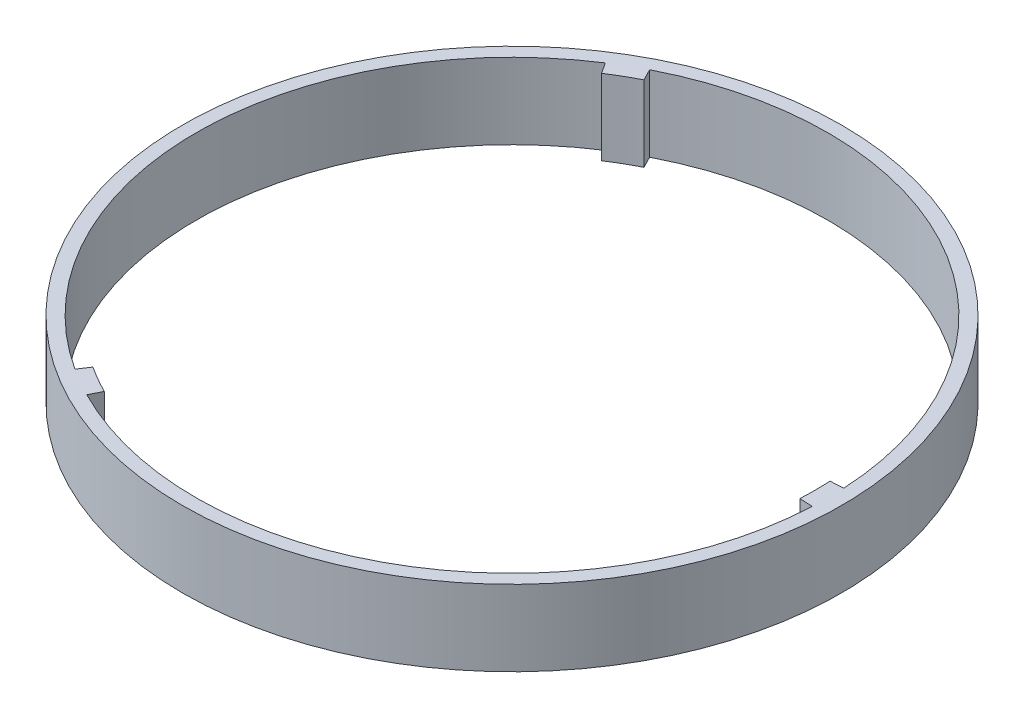
SolidWorks part; units mm, degrees
ref_plane "Front Plane" through (0, 0, 0) normal (0, 0, 1) x (1, 0, 0)
ref_plane "Top Plane" through (0, 0, 0) normal (0, 1, 0) x (1, 0, 0)
ref_plane "Right Plane" through (0, 0, 0) normal (1, 0, 0) x (0, 0, -1)
sketch "Sketch1" plane through (0, 0, 0) normal (0, 1, 0) x (1, 0, 0)
  circle A0 centre (0, 0) radius 110.49
  dimension "D1" = 220.98
extrude "Boss-Extrude1" add sketch "Sketch1" along normal blind 25.4
sketch "Sketch2" plane through (0, 25.4, 0) normal (0, 1, 0) x (1, 0, 0)
  circle A0 centre (0, 0) radius 101.6
extrude "Cut-Extrude6" cut sketch "Sketch2" against normal blind 64.52
sketch "Sketch5" plane through (0, 25.4, 0) normal (0, 1, 0) x (1, 0, 0)
  line L0 (-110.49, 0) -> (110.49, 0) construction
  line L1 (0, 0) -> (-55.2498, 95.6844) construction
  line L2 (0, 0) -> (-55.245, -95.6871) construction
  line L3 (-46.2337, -90.471) -> (-55.2333, -85.2751)
  line L5 (-46.2337, -90.471) -> (-55.2333, -85.2751) construction
  line L8 (-46.2337, -90.471) -> (-48.2094, -94.3533)
  line L9 (110.49, 0) -> (101.4685, 5.1668) construction
  line L10 (110.49, 0) -> (101.4785, -4.9664) construction
  line L11 (101.4685, 5.1668) -> (101.4785, -4.9664)
  line L12 (101.4785, -4.9664) -> (105.8294, -5.1794)
  line L13 (101.4685, 5.1668) -> (105.819, 5.3883)
  line L14 (101.4785, -4.9664) -> (110.3587, -5.385) construction
  line L15 (101.4685, 5.1668) -> (110.3451, 5.6561) construction
  line L16 (-55.2333, -85.2751) -> (-57.6015, -88.9312)
  line L17 (-55.2498, 95.6844) -> (-46.2253, 90.4753) construction
  line L18 (-55.2499, 85.2644) -> (-46.2253, 90.4753)
  line L19 (-46.2253, 90.4753) -> (-48.2072, 94.3545)
  line L20 (-55.2499, 85.2644) -> (-57.6187, 88.9201)
  line L21 (-55.2499, 85.2644) -> (-60.0842, 92.725) construction
  line L22 (-46.2253, 90.4753) -> (-50.27, 98.3919) construction
  circle A0 centre (0, 0) radius 101.6
  circle A1 centre (0, 0) radius 110.49 construction
  arc A2 (-48.2094, -94.3533) -> (105.8294, -5.1794) centre (0, 0) ccw
  arc A3 (105.819, 5.3883) -> (-48.2072, 94.3545) centre (0, 0) ccw
  circle A5 centre (0, 0) radius 101.6 construction
  arc A6 (-57.6187, 88.9201) -> (-57.6015, -88.9312) centre (0, 0) ccw
  spline S1 degree 2 poles (-57.6015, -88.9312) (-58.9889, -88.0326) (-60.3491, -87.0901) knots 0.766293 0.766293 0.766293 1 1 1
extrude "Cut-Extrude7" cut sketch "Sketch5" against normal blind 64.52 contours A2 L12 L11 L13 A3 L19 L18 L20 A6 L16 L3 L8
scale "Scale1" scale about centroid uniform scaling yes scale factor 0.5
